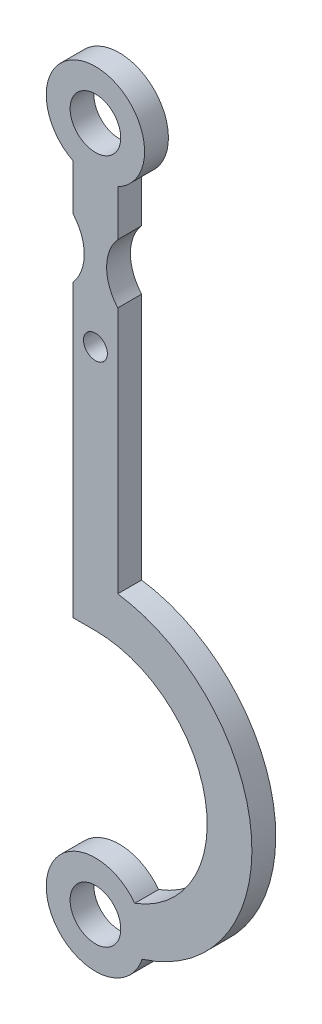
SolidWorks part; units mm, degrees
material "1.0577 (S355J2G4)"
ref_plane "Front Plane" through (0, 0, 0) normal (0, 0, 1) x (1, 0, 0)
ref_plane "Top Plane" through (0, 0, 0) normal (0, 1, 0) x (1, 0, 0)
ref_plane "Right Plane" through (0, 0, 0) normal (1, 0, 0) x (0, 0, -1)
sketch "Sketch1" plane through (0, 0, 0) normal (0, 0, 1) x (1, 0, 0)
  line L0 (-7.5, -14.6969) -> (-7.5, -30.0784)
  line L1 (7.5, -14.6969) -> (7.5, -30.0784)
  line L2 (0, 0) -> (0, -87.0636) construction
  line L3 (-7.5, -49.9216) -> (-7.5, -148.2398)
  line L4 (7.5, -49.9216) -> (7.5, -133.0208)
  line L5 (0, -147.4825) -> (-7.5, -147.4825)
  line L6 (15.6854, -235.1204) -> (13.2109, -220.1146) construction
  circle A0 centre (0, 0) radius 8.5
  arc A1 (-7.5, -14.6969) -> (7.5, -14.6969) centre (0, 0) cw
  arc A2 (-7.5, -30.0784) -> (-7.5, -49.9216) centre (-18.75, -40) cw
  arc A3 (7.5, -30.0784) -> (7.5, -49.9216) centre (18.75, -40) ccw
  arc A4 (-7.5, -148.2398) -> (13.2109, -220.1146) centre (0, -185) cw
  arc A5 (13.2109, -220.1146) -> (15.6854, -235.1204) centre (0, -230) ccw
  arc A6 (15.6854, -235.1204) -> (7.5, -133.0208) centre (0, -185) ccw
  circle A7 centre (0, -230) radius 8.5
  arc A8 (0, -230) -> (0, -140) centre (0, -185) ccw construction
  circle A9 centre (0, -65) radius 4
  point P11 (-3.75, -40)
  point P21 (14.4482, -227.6175)
  point P25 (3.75, -40)
  dimension "D1" = 17
  dimension "D2" = 8
  dimension "D3" = 17
  dimension "D4" = 15
  dimension "D7" = 230
  dimension "D9" = 8
  dimension "D11" = 15
  dimension "D12" = 185
  dimension "D13" = 8
  dimension "D10" = 65
  dimension "D5" = 7.5
  dimension "D6" = 15
  dimension "D8" = 40
extrude "Boss-Extrude1" add sketch "Sketch1" along normal blind 8 contours A5 A6 L4 A3 L1 A1 L0 A2 L3 L5 A4 A7 A0
sketch "Sketch2" plane through (0, 0, 8) normal (0, 0, 1) x (1, 0, 0)
  line L0 (-7.5, -95) -> (-6, -92.4)
  line L1 (-7.5, -49.9216) -> (-7.5, -147.4825) construction
  line L2 (-6, -92.4) -> (-6, -99.5)
  line L3 (-6, -99.5) -> (-5.5, -100)
  line L4 (-5.5, -100) -> (-2.5, -100)
  line L7 (-5.5, -100) -> (-6, -100.5)
  line L8 (-6, -100.5) -> (-6, -107.6)
  line L9 (-6, -107.6) -> (-7.5, -105)
  line M16 (-7.5, -49.9216) -> (-7.5, -147.4825)
  dimension "D1" = 10
  dimension "D2" = 1.5
  dimension "D3" = 2
  dimension "D4" = 1
  dimension "D5" = 7.6
  dimension "D6" = 5
  dimension "D7" = 100
extrude "Cut-Extrude1" [suppressed] cut sketch "Sketch2" against normal through all contours L9 L8 L7 L3 L2 L0 M16
fillet "Fillet1" [suppressed] radius 5
